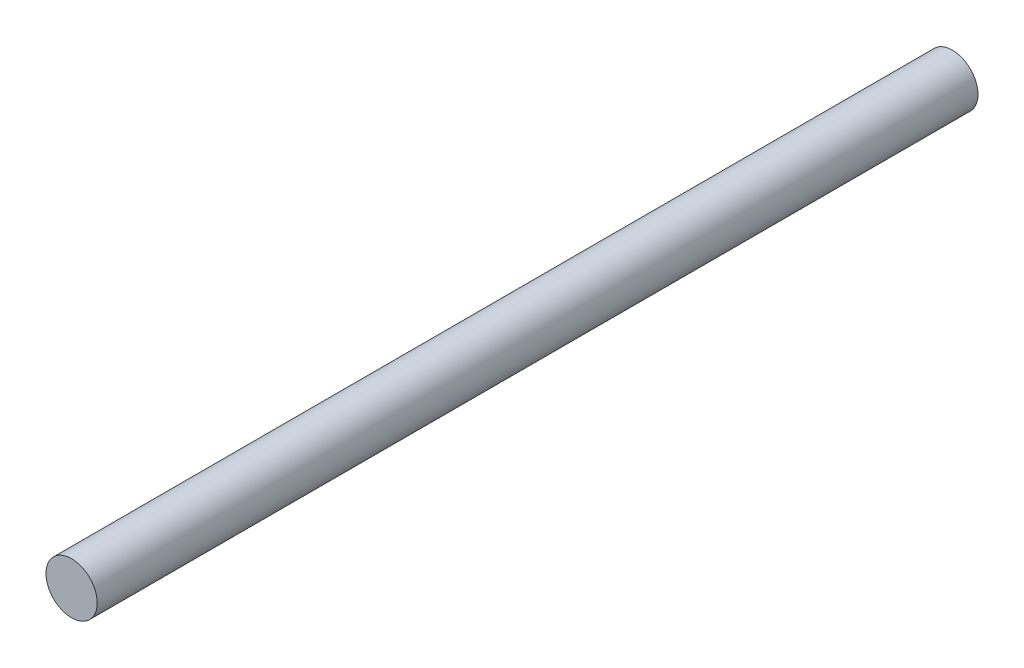
SolidWorks part; units mm, degrees
ref_plane "Front Plane" through (0, 0, 0) normal (0, 0, 1) x (1, 0, 0)
ref_plane "Top Plane" through (0, 0, 0) normal (0, 1, 0) x (1, 0, 0)
ref_plane "Right Plane" through (0, 0, 0) normal (1, 0, 0) x (0, 0, -1)
sketch "Sketch1" plane through (0, 0, 0) normal (0, 0, 1) x (1, 0, 0)
  circle A0 centre (0, 0) radius 4
  dimension "D1" = 8
extrude "Boss-Extrude1" add sketch "Sketch1" along normal blind 137.5
move or copy body "Body-Move/Copy1" [suppressed] bodies to move or copy 101
